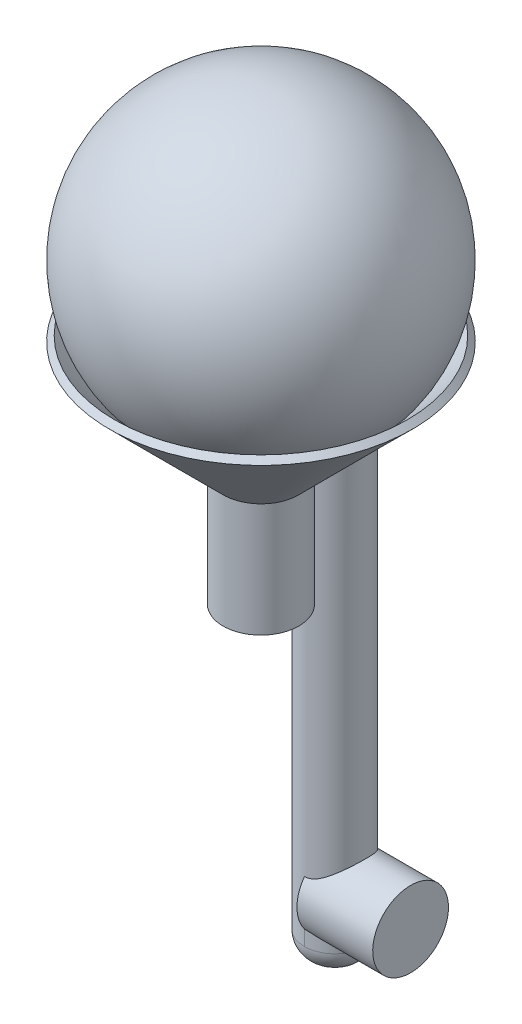
SolidWorks part; units mm, degrees
ref_plane "Front Plane" through (0, 0, 0) normal (0, 0, 1) x (1, 0, 0)
ref_plane "Top Plane" through (0, 0, 0) normal (0, 1, 0) x (1, 0, 0)
ref_plane "Right Plane" through (0, 0, 0) normal (1, 0, 0) x (0, 0, -1)
sketch "Sketch1" plane through (0, 0, 0) normal (0, 0, 1) x (1, 0, 0)
  line L0 (0, 0) -> (0, 24.3198) construction
  line L1 (-5, 0) -> (-5, -15)
  line L2 (-5, 0) -> (-20, 15)
  line L3 (-4, 0) -> (-4, -15)
  line L5 (-5, -15) -> (-4, -15)
  line L6 (-20, 15) -> (-19.2929, 15.7071)
  line L7 (-16.2592, 12.6734) -> (-19.2929, 15.7071)
  line L8 (-4, 0) -> (0, 0)
  line L9 (-4, 0.4142) -> (-19.2929, 15.7071) construction
  line L10 (0, 0) -> (0, 44.3198)
  line L11 (-4, 0.4142) -> (-4, -15) construction
  arc A0 (-16.2592, 12.6734) -> (0, 44.3198) centre (0, 24.3198) cw
  dimension "D6" = 20
  dimension "D1" = 5
  dimension "D2" = 135
  dimension "D3" = 15
  dimension "D4" = 15
  dimension "D5" = 1
revolve "Revolve1" add sketch "Sketch1" angle 360 about L10
sketch "Sketch2" plane through (0, 0, 0) normal (0, 1, 0) x (1, 0, 0)
  line L0 (0, -22) -> (0, 22) construction
  circle A0 centre (0, 9.7477) radius 4
  dimension "D1" = 8
extrude "Boss-Extrude1" add sketch "Sketch2" along normal up to next and the other way blind 60
fillet "Fillet1" radius 3 1 edges at (0, -60, -5.7477)
sketch "Sketch3" plane through (0, 0, 0) normal (1, 0, 0) x (0, 0, -1)
  line L0 (5.7477, -57) -> (13.7477, -57) construction
  circle A0 centre (9.7477, -52) radius 5
  point P2 (9.7903, -57.1989)
  dimension "D1" = 10
  dimension "D2" = 5
extrude "Boss-Extrude2" add sketch "Sketch3" along normal blind 10
